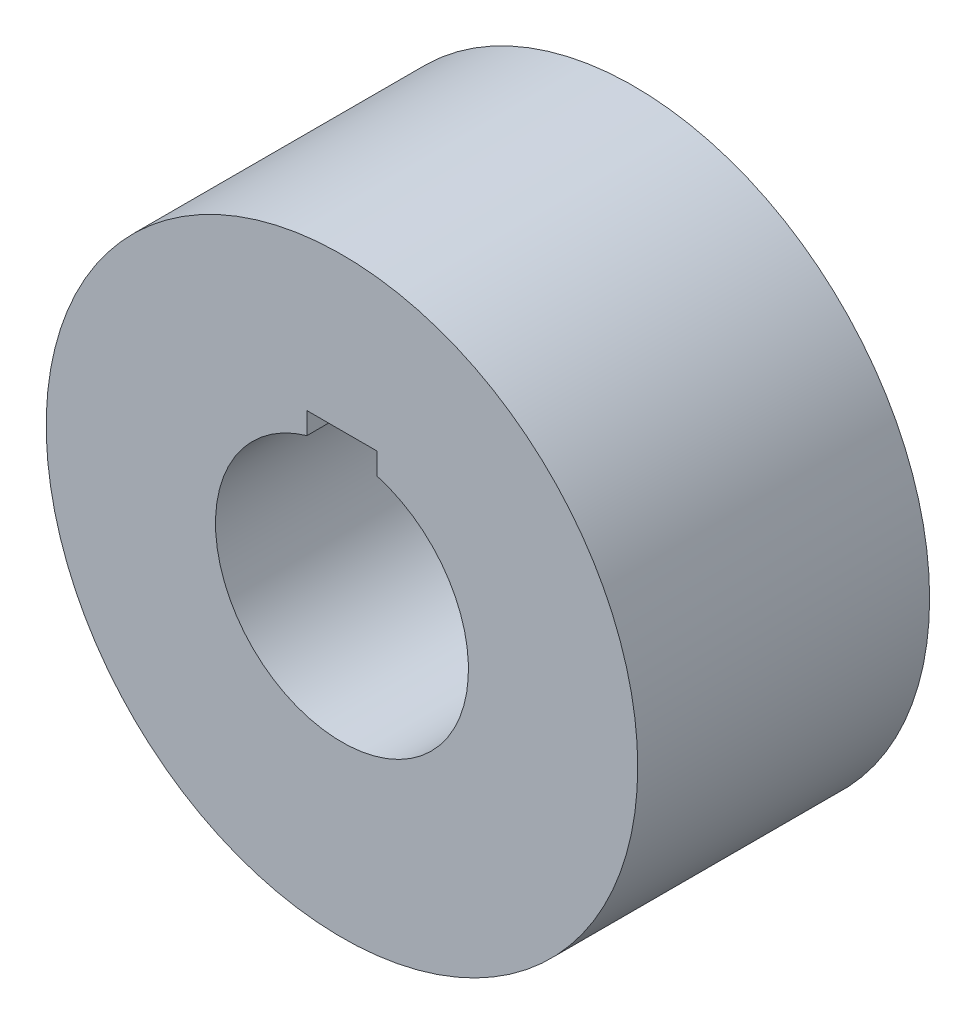
SolidWorks part; units mm, degrees
material "Plain Carbon Steel"
ref_plane "Front Plane" through (0, 0, 0) normal (0, 0, 1) x (1, 0, 0)
ref_plane "Top Plane" through (0, 0, 0) normal (0, 1, 0) x (1, 0, 0)
ref_plane "Right Plane" through (0, 0, 0) normal (1, 0, 0) x (0, 0, -1)
sketch "Sketch1" plane through (0, 0, 0) normal (0, 0, 1) x (1, 0, 0)
  line L2 (-9, 31.229) -> (-9, 36.8)
  line L3 (-9, 36.8) -> (9, 36.8)
  line L4 (9, 31.229) -> (9, 36.8)
  circle A0 centre (0, 0) radius 76
  arc A1 (-9, 31.229) -> (9, 31.229) centre (0, 0) ccw
  point P8 (0, 36.8)
  point P9 (0, 32.5)
  dimension "D2" = 65
  dimension "D4" = 152
  dimension "D1" = 18
  dimension "D3" = 4.3
extrude "Boss-Extrude1" add sketch "Sketch1" along normal blind 75
